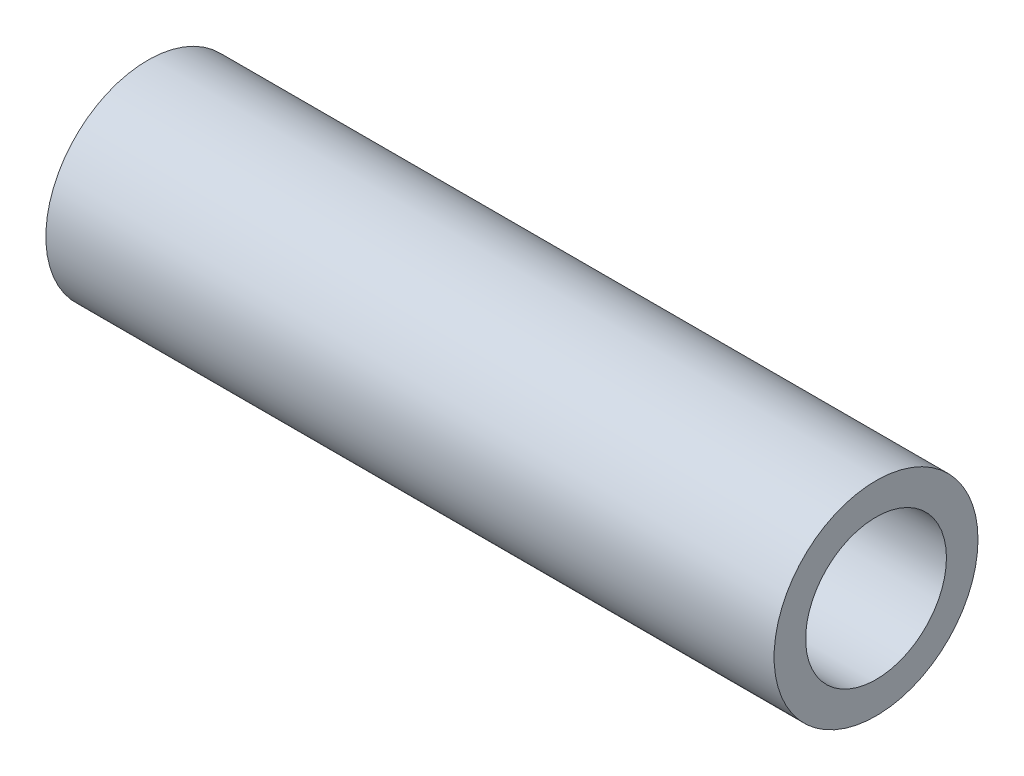
SolidWorks part; units mm, degrees
material "PVC 0.007 Plasticized"
ref_plane "Front Plane" through (0, 0, 0) normal (0, 0, 1) x (1, 0, 0)
ref_plane "Top Plane" through (0, 0, 0) normal (0, 1, 0) x (1, 0, 0)
ref_plane "Right Plane" through (0, 0, 0) normal (1, 0, 0) x (0, 0, -1)
sketch "Sketch1" plane through (0, 0, 0) normal (1, 0, 0) x (0, 0, -1)
  circle A0 centre (0, 0) radius 10.668
  circle A1 centre (0, 0) radius 7.366
  dimension "D1" = 21.336
  dimension "D2" = 14.732
extrude "Boss-Extrude1" add sketch "Sketch1" against normal blind 76.2
